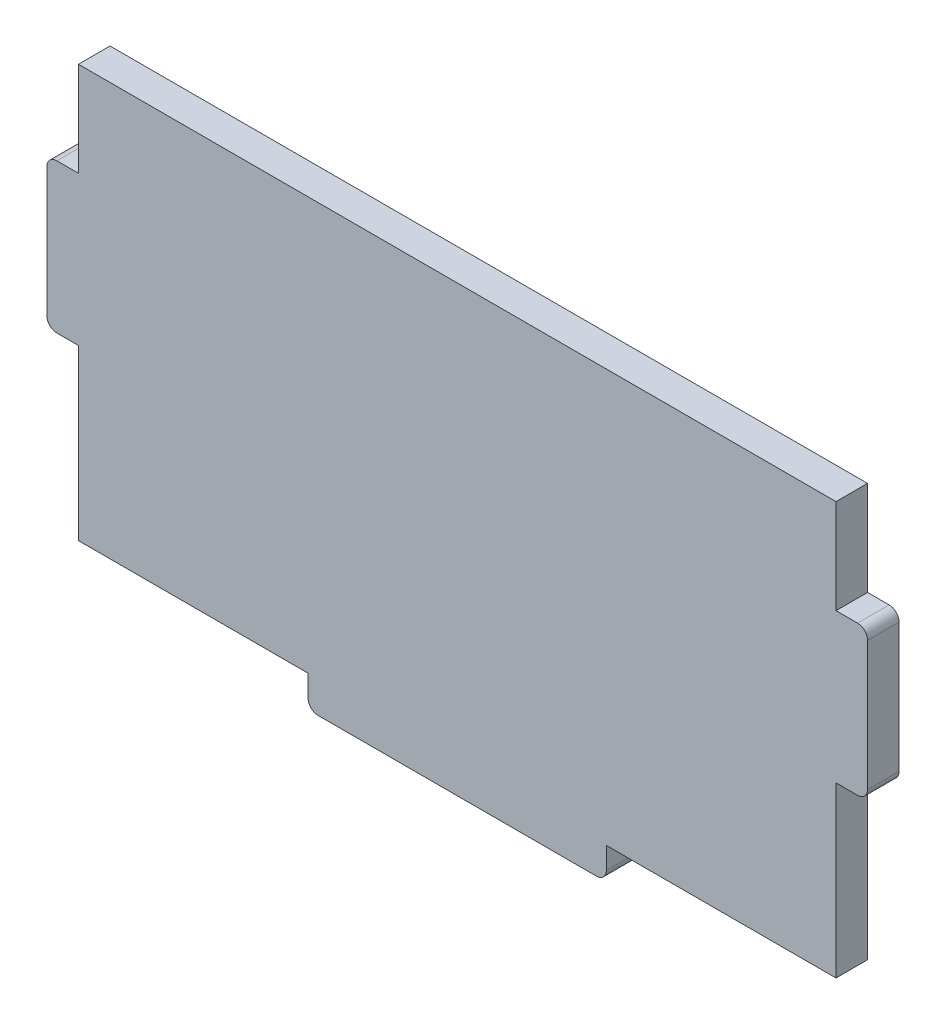
SolidWorks part; units mm, degrees
ref_plane "Front Plane" through (0, 0, 0) normal (0, 0, 1) x (1, 0, 0)
ref_plane "Top Plane" through (0, 0, 0) normal (0, 1, 0) x (1, 0, 0)
ref_plane "Right Plane" through (0, 0, 0) normal (1, 0, 0) x (0, 0, -1)
sketch "Sketch1" plane through (0, 0, 0) normal (0, 0, 1) x (1, 0, 0)
  line L1 (-38.1, -20.75) -> (38.1, -20.75)
  line L2 (-38.1, -20.75) -> (-38.1, 20.75)
  line L3 (-38.1, 20.75) -> (38.1, 20.75)
  line L4 (38.1, -20.75) -> (38.1, 20.75)
  line L5 (-38.1, -20.75) -> (38.1, 20.75) construction
  line L6 (-38.1, 20.75) -> (38.1, -20.75) construction
  point P0 (0, 0)
  point P6 (38.1, 0)
  dimension "D1" = 41.5
  dimension "D2" = 76.2
extrude "Boss-Extrude1" add sketch "Sketch1" along normal blind 3.175
sketch "Sketch2" plane through (38.1, 0, 0) normal (1, 0, 0) x (0, 0, -1)
  line L0 (-3.175, -20.75) -> (-3.175, 20.75) construction
  line L1 (-3.175, 11.25) -> (0, 11.25)
  line L2 (-3.175, 11.25) -> (-3.175, -3.75)
  line L3 (-3.175, -3.75) -> (0, -3.75)
  line L4 (0, 11.25) -> (0, -3.75)
  line L5 (0, -20.75) -> (0, 20.75) construction
  line L6 (-3.175, -20.75) -> (0, -20.75) construction
  point P10 (-1.5875, -20.75)
  point P11 (-1.5875, 11.25)
  dimension "D1" = 17
  dimension "D2" = 15
extrude "Boss-Extrude2" add sketch "Sketch2" along normal blind 3.175
sketch "Sketch4" plane through (0, -20.75, 0) normal (0, -1, 0) x (1, 0, 0)
  line L0 (-38.1, 3.175) -> (38.1, 3.175) construction
  line L1 (-15, 3.175) -> (15, 3.175)
  line L2 (-15, 3.175) -> (-15, 0)
  line L3 (-15, 0) -> (15, 0)
  line L4 (15, 3.175) -> (15, 0)
  line L5 (0, 0) -> (0, -2.2945) construction
  point P6 (0, 0)
  dimension "D1" = 30
extrude "Boss-Extrude4" add sketch "Sketch4" along normal blind 3.175
sketch "Sketch5" plane through (-38.1, 0, 0) normal (-1, 0, 0) x (0, 0, 1)
  line L0 (0, 20.75) -> (0, -20.75) construction
  line L1 (0, 11.25) -> (3.175, 11.25)
  line L2 (0, 11.25) -> (0, -3.75)
  line L3 (0, -3.75) -> (3.175, -3.75)
  line L4 (3.175, 11.25) -> (3.175, -3.75)
  line L5 (3.175, 20.75) -> (3.175, -20.75) construction
  line L7 (3.175, -20.75) -> (0, -20.75) construction
  dimension "D1" = 15
  dimension "D2" = 17
extrude "Boss-Extrude5" add sketch "Sketch5" along normal blind 3.175
fillet "Fillet1" radius 1 6 edges at (41.275, 11.25, 1.5875) (41.275, -3.75, 1.5875) (15, -23.925, 1.5875) (-15, -23.925, 1.5875) (-41.275, -3.75, 1.5875) (-41.275, 11.25, 1.5875)
